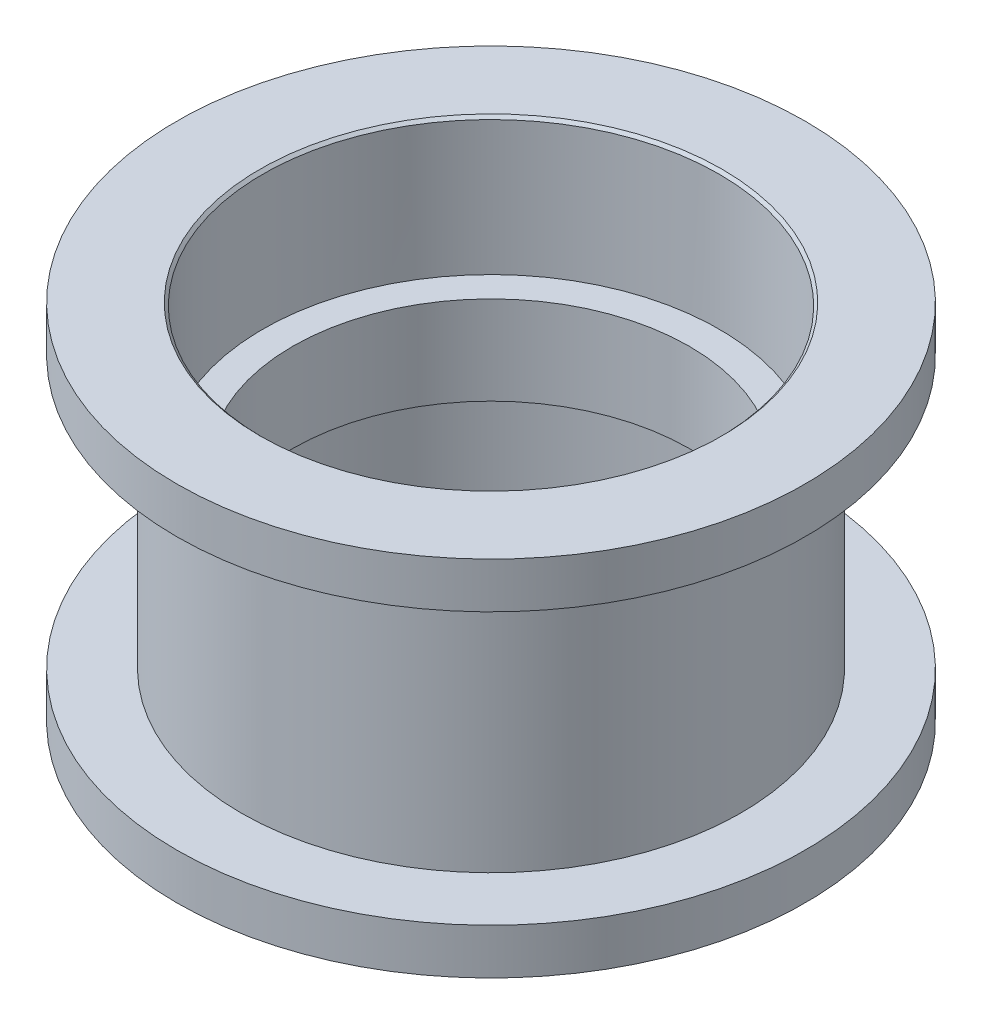
SolidWorks part; units mm, degrees
material "Delrin 2700 NC010, Low Viscosity Acetal Copolymer (SS)"
ref_plane "Front Plane" through (0, 0, 0) normal (0, 0, 1) x (1, 0, 0)
ref_plane "Top Plane" through (0, 0, 0) normal (0, 1, 0) x (1, 0, 0)
ref_plane "Right Plane" through (0, 0, 0) normal (1, 0, 0) x (0, 0, -1)
sketch "Sketch2" plane through (0, 0, 0) normal (0, 0, 1) x (1, 0, 0)
  line L0 (0, 30.4981) -> (0, -27.9967) construction
  line L1 (6.945, -1.55) -> (6.945, 1.55)
  line L2 (6.945, 1.55) -> (7.9875, 1.55)
  line L3 (7.9875, 1.55) -> (7.9875, 6.35)
  line L4 (7.9875, 6.35) -> (11, 6.35)
  line L5 (11, 6.35) -> (11, 4.75)
  line L6 (11, 4.75) -> (8.75, 4.75)
  line L7 (8.75, 4.75) -> (8.75, -4.75)
  line L8 (0, 0) -> (8.75, 0) construction
  line L9 (11, -4.75) -> (8.75, -4.75)
  line L10 (11, -6.35) -> (11, -4.75)
  line L11 (7.9875, -6.35) -> (11, -6.35)
  line L12 (7.9875, -1.55) -> (7.9875, -6.35)
  line L13 (6.945, -1.55) -> (7.9875, -1.55)
  point P18 (6.945, 0)
  dimension "D1" = 11
  dimension "D2" = 1.6
  dimension "D3" = 7.9875
  dimension "D4" = 8.75
  dimension "D5" = 6.945
  dimension "D6" = 1.55
  dimension "D7" = 6.35
revolve "Revolve1" add sketch "Sketch2" angle 360 about L0
chamfer "Chamfer1" distance 0.1 angle 45 1 edges at (0, 6.35, 7.9875)
chamfer "Chamfer2" distance 0.1 angle 45 1 edges at (0, -6.35, 7.9875)
ref_plane "Plane1" through (0, 0, 0) normal (0, -1, 0) x (-1, 0, 0)
